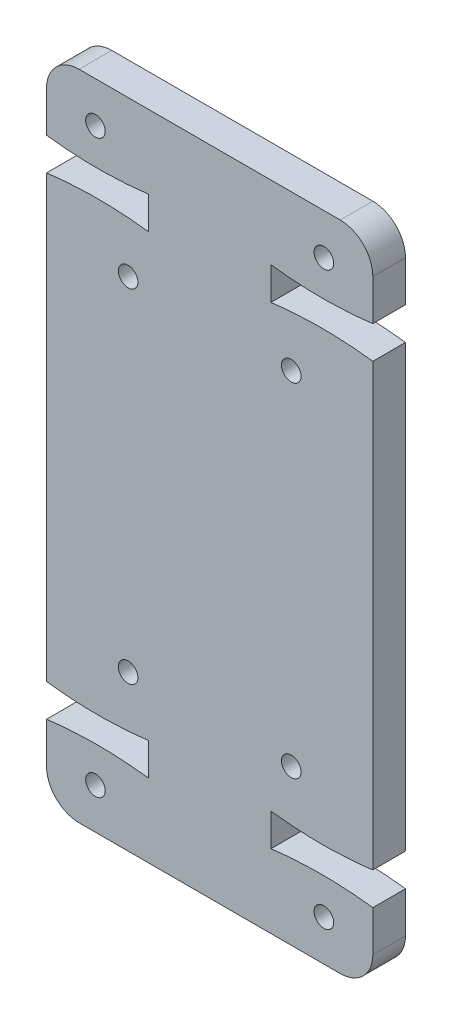
SolidWorks part; units mm, degrees
ref_plane "Front Plane" through (0, 0, 0) normal (0, 0, 1) x (1, 0, 0)
ref_plane "Top Plane" through (0, 0, 0) normal (0, 1, 0) x (1, 0, 0)
ref_plane "Right Plane" through (0, 0, 0) normal (1, 0, 0) x (0, 0, -1)
sketch "Sketch1" plane through (0, 0, 0) normal (0, 0, 1) x (1, 0, 0)
  line L0 (0, 6.5) -> (0, 33.5)
  line L1 (0, 0) -> (20, 0)
  line L2 (0, 35.5) -> (0, 40)
  line L3 (10, 40) -> (10, 0) construction
  line L4 (0, 20) -> (20, 20) construction
  line L5 (0, 4.5) -> (6.25, 4.5) construction
  line L6 (6.25, 4.5) -> (6.25, 6.5)
  line L7 (6.25, 6.5) -> (0, 6.5) construction
  line L8 (0, 4.5) -> (0, 0)
  line L9 (6.25, 33.5) -> (0, 33.5) construction
  line L10 (6.25, 35.5) -> (6.25, 33.5)
  line L11 (0, 35.5) -> (6.25, 35.5) construction
  line L12 (0, 40) -> (20, 40)
  line L13 (20, 35.5) -> (13.75, 35.5) construction
  line L14 (13.75, 35.5) -> (13.75, 33.5)
  line L15 (13.75, 33.5) -> (20, 33.5) construction
  line L16 (20, 4.5) -> (20, 0)
  line L17 (13.75, 6.5) -> (20, 6.5) construction
  line L18 (13.75, 4.5) -> (13.75, 6.5)
  line L19 (20, 4.5) -> (13.75, 4.5) construction
  line L20 (20, 35.5) -> (20, 40)
  line L21 (20, 6.5) -> (20, 33.5)
  line L22 (3.125, 4.5) -> (3.125, 4.7) construction
  line L23 (6.25, 5.5) -> (0, 5.5) construction
  circle A0 centre (3, 2.5) radius 0.6
  circle A1 centre (5, 9.5) radius 0.6
  circle A2 centre (5, 30.5) radius 0.6
  circle A3 centre (3, 37.5) radius 0.6
  circle A4 centre (17, 37.5) radius 0.6
  circle A5 centre (15, 30.5) radius 0.6
  circle A6 centre (15, 9.5) radius 0.6
  circle A7 centre (17, 2.5) radius 0.6
  spline S0 degree 2 poles (0, 4.5) (3.125, 4.9) (6.25, 4.5) knots 0 0 0 1 1 1
  spline S1 degree 2 poles (0, 6.5) (3.125, 6.1) (6.25, 6.5) knots 0 0 0 1 1 1
  spline S2 degree 2 poles (20, 4.5) (16.875, 4.9) (13.75, 4.5) knots 0 0 0 1 1 1
  spline S3 degree 2 poles (20, 6.5) (16.875, 6.1) (13.75, 6.5) knots 0 0 0 1 1 1
  spline S4 degree 2 poles (20, 35.5) (16.875, 35.1) (13.75, 35.5) knots 0 0 0 1 1 1
  spline S5 degree 2 poles (20, 33.5) (16.875, 33.9) (13.75, 33.5) knots 0 0 0 1 1 1
  spline S6 degree 2 poles (0, 35.5) (3.125, 35.1) (6.25, 35.5) knots 0 0 0 1 1 1
  spline S7 degree 2 poles (0, 33.5) (3.125, 33.9) (6.25, 33.5) knots 0 0 0 1 1 1
  point P23 (10, 20)
  dimension "D1" = 1.2
  dimension "D2" = 3
  dimension "D3" = 2.5
  dimension "D4" = 4.5
  dimension "D5" = 2
  dimension "D6" = 6.25
  dimension "D7" = 5
  dimension "D8" = 9.5
  dimension "D9" = 10
  dimension "D10" = 20
  dimension "D11" = 0.2
extrude "Finger PIP Body" add sketch "Sketch1" along normal blind 2
fillet "Finger PIP Contouring" radius 2 4 edges at (0, 40, 1) (20, 40, 1) (20, 0, 1) (0, 0, 1)
equation "\"D10@Sketch1\"=\"Lp@Parameters@RobotHandParameters.SLDPRT\"/2"
equation "\"D9@Sketch1\"=\"Wph@Parameters@RobotHandParameters.SLDPRT\"/2"
equation "\"D11@Sketch1\"=\"radii_fit@Parameters@RobotHandParameters.SLDPRT\""
equation "\"D1@Sketch1\"=1+\"cut_free@Parameters@RobotHandParameters.SLDPRT\""
